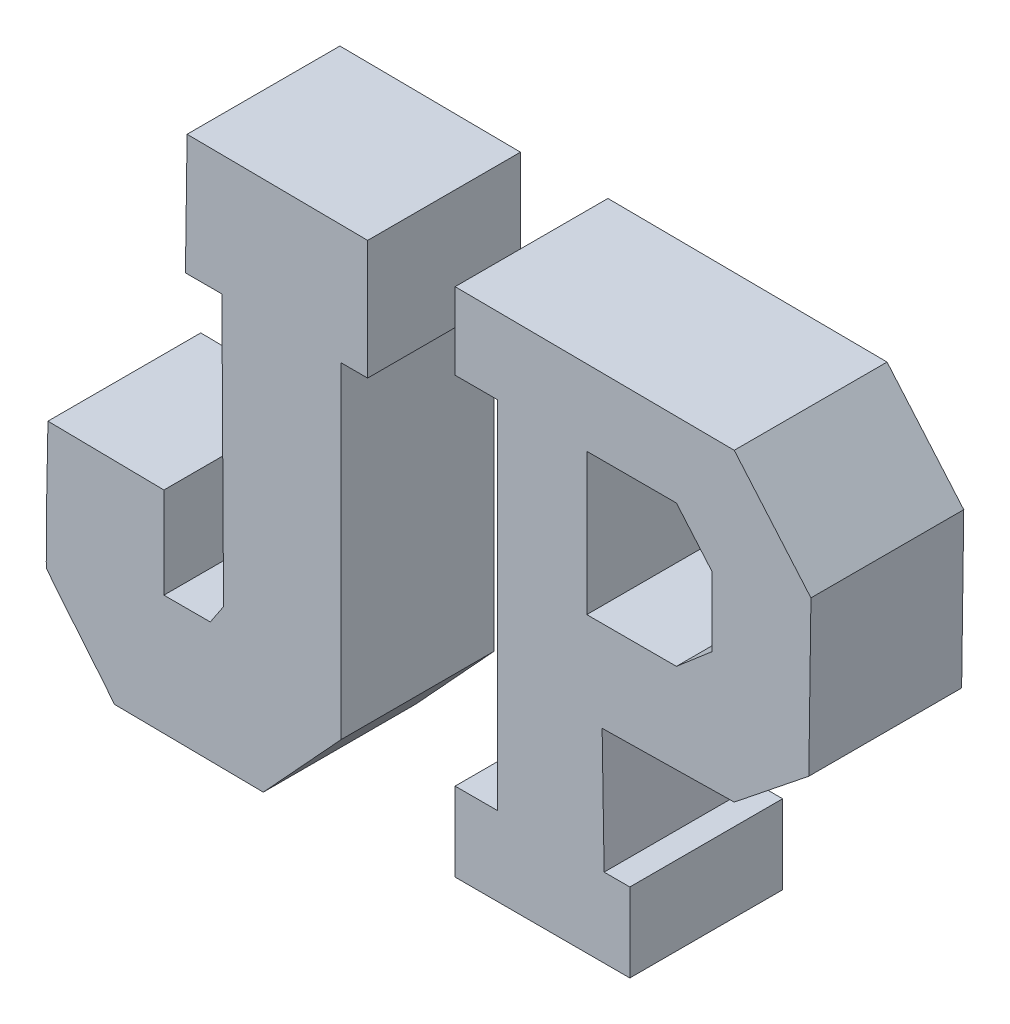
SolidWorks part; units mm, degrees
ref_plane "Front Plane" through (0, 0, 0) normal (0, 0, 1) x (1, 0, 0)
ref_plane "Top Plane" through (0, 0, 0) normal (0, 1, 0) x (1, 0, 0)
ref_plane "Right Plane" through (0, 0, 0) normal (1, 0, 0) x (0, 0, -1)
sketch "Sketch2" plane through (0, 0, 0) normal (0, 0, 1) x (1, 0, 0)
  line L0 (55.8333, 244) -> (279.1667, 244) construction
  line L1 (55.8333, 244) -> (279.1667, 244) construction
  line L2 (41.4514, 78.6271) -> (62.7178, 78.432)
  line L3 (62.7178, 78.432) -> (62.7178, 64.3845)
  line L4 (62.7178, 64.3845) -> (59.5961, 64.3845)
  line L5 (59.5961, 64.3845) -> (59.5961, 25.9489)
  line L6 (25.0626, 41.167) -> (38.7199, 40.9719)
  line L7 (59.5961, 25.9489) -> (50.4262, 15.9986)
  line L8 (50.4262, 15.9986) -> (32.8668, 16.1937)
  line L9 (38.7199, 40.9719) -> (38.7199, 30.2412)
  line L10 (38.7199, 30.2412) -> (44.1829, 30.2412)
  line L11 (44.1829, 30.2412) -> (45.7437, 32.5825)
  line L12 (45.7437, 32.5825) -> (45.5486, 64.3845)
  line L13 (45.5486, 64.3845) -> (41.2563, 64.3845)
  line L14 (41.2563, 64.3845) -> (41.4514, 78.6271)
  line L15 (133.6964, 60.4813) -> (333.6964, 60.4813) construction
  line L16 (105.0967, 161.1016) -> (305.0967, 161.1016) construction
  line L17 (73.0214, 78.8625) -> (105.898, 78.6116)
  line L18 (114.9328, 68.071) -> (114.6818, 49.7504)
  line L19 (114.6818, 49.7504) -> (105.898, 42.7234)
  line L20 (105.898, 42.7234) -> (90.338, 42.4724)
  line L21 (90.338, 42.4724) -> (90.5728, 27.9163)
  line L22 (90.5728, 27.9163) -> (93.6006, 27.9163)
  line L23 (73.0214, 18.6306) -> (93.6006, 18.6306)
  line L24 (78.0407, 27.9163) -> (78.0407, 69.8277)
  line L25 (78.0407, 27.9163) -> (73.0214, 27.9163)
  line L26 (93.6006, 18.6306) -> (93.6006, 27.9163)
  line L27 (78.0407, 69.8277) -> (73.0214, 69.8277)
  line L28 (73.0214, 18.6306) -> (73.0214, 27.9163)
  line L29 (73.0214, 69.8277) -> (73.0214, 78.8625)
  line L30 (105.898, 78.6116) -> (114.9328, 68.071)
  line L32 (88.5303, 69.8277) -> (88.5303, 53.1645)
  line L35 (99.0862, 69.8277) -> (103.2688, 64.9481)
  line L36 (88.5303, 69.8277) -> (99.0862, 69.8277)
  line L38 (88.5303, 53.1645) -> (99.0862, 53.1645)
  line L39 (99.0862, 53.1645) -> (103.2688, 56.7495)
  line L40 (103.2688, 56.7495) -> (103.2688, 64.9481)
  spline S0 degree 3 poles (32.8668, 16.1937) (31.9106, 17.628) (24.8725, 25.7517) (24.8675, 26.144) (24.8041, 31.1517) (24.9976, 36.1594) (25.0626, 41.167) knots 0 0 0 0 1 1 1 2 2 2 2
extrude "Boss-Extrude1" add sketch "Sketch2" along normal blind 18
